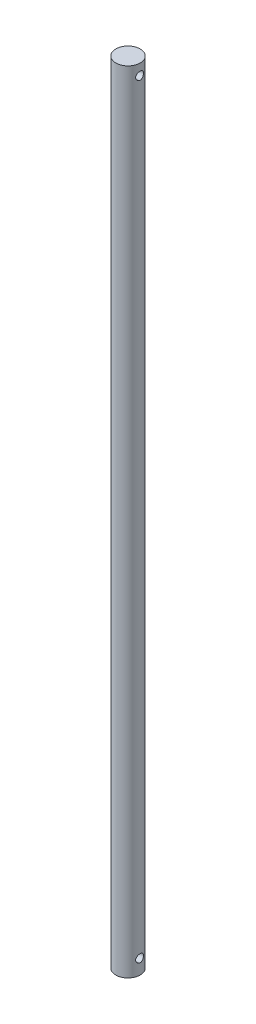
SolidWorks part; units mm, degrees
material "1060 Alloy"
ref_plane "Front Plane" through (0, 0, 0) normal (0, 0, 1) x (1, 0, 0)
ref_plane "Top Plane" through (0, 0, 0) normal (0, 1, 0) x (1, 0, 0)
ref_plane "Right Plane" through (0, 0, 0) normal (1, 0, 0) x (0, 0, -1)
sketch "Sketch1" plane through (0, 0, 0) normal (1, 0, 0) x (0, 0, -1)
  line L1 (0, 0) -> (-10, 0)
  line L2 (0, 0) -> (0, 647.7)
  line L3 (0, 647.7) -> (-10, 647.7)
  line L4 (-10, 0) -> (-10, 647.7)
  circle A0 centre (0, 638.7) radius 3.2
  circle A1 centre (0, 12) radius 3.2
  dimension "D3" = 6.4
  dimension "D4" = 6.4
  dimension "D1" = 647.7
  dimension "D2" = 10
  dimension "D5" = 9
  dimension "D6" = 12
revolve "Revolve2" add sketch "Sketch1" angle 360 about L2
sketch "Sketch2" plane through (0, 0, 0) normal (1, 0, 0) x (0, 0, -1)
  line L0 (-10, 0) -> (10, 0) construction
  line L1 (10, 647.7) -> (-10, 647.7) construction
  line L2 (0, 12) -> (0, 638.7) construction
  line L3 (10, 0) -> (10, 647.7) construction
  circle A0 centre (0, 638.7) radius 3.2
  circle A1 centre (0, 12) radius 3.2
  dimension "D1" = 6.4
  dimension "D2" = 6.4
  dimension "D3" = 12
  dimension "D4" = 9
  dimension "D5" = 10
extrude "Cut-Extrude1" cut sketch "Sketch2" against normal through all both and the other way through all
